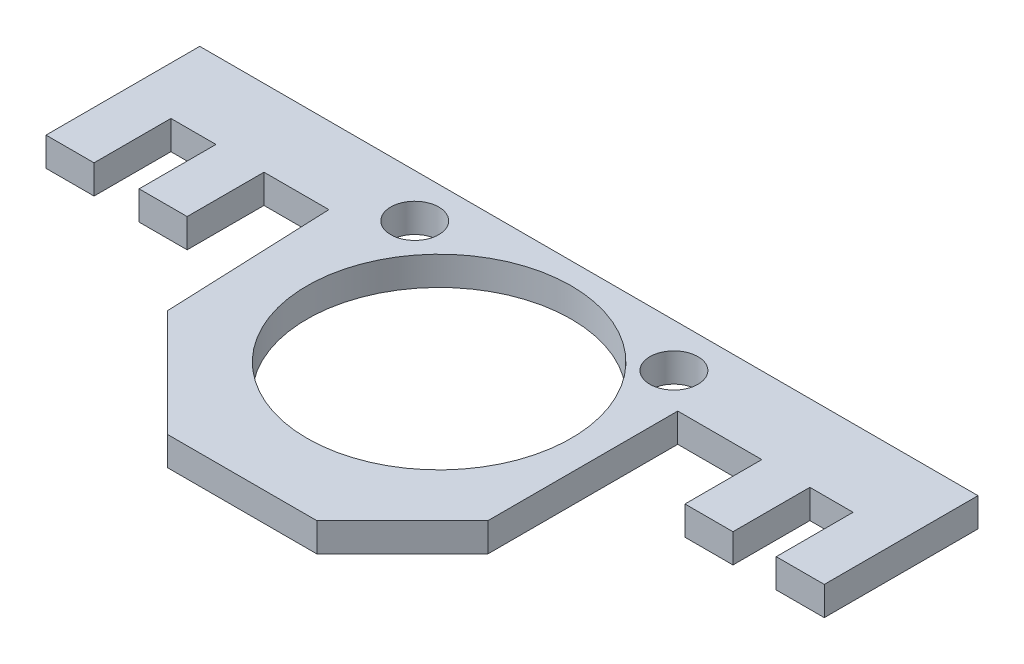
SolidWorks part; units mm, degrees
ref_plane "Front" through (0, 0, 0) normal (0, 0, 1) x (1, 0, 0)
ref_plane "Top" through (0, 0, 0) normal (0, 1, 0) x (1, 0, 0)
ref_plane "Right" through (0, 0, 0) normal (1, 0, 0) x (0, 0, -1)
sketch "Sketch1" plane through (0, 0, 0) normal (0, 1, 0) x (1, 0, 0)
  line L0 (-54.5899, 21.7003) -> (-22.1899, 21.7003)
  line L1 (-54.5899, 21.7003) -> (-54.5899, 15.3003)
  line L2 (-22.1899, 21.7003) -> (-22.1899, 15.3003)
  line L3 (-22.1899, 15.3003) -> (-24.1899, 15.3003)
  line L4 (-54.5899, 15.3003) -> (-52.5899, 15.3003)
  line L5 (-52.5899, 15.3003) -> (-52.5899, 18.5003)
  line L6 (-52.5899, 18.5003) -> (-50.714, 18.5003)
  line L7 (-50.714, 18.5003) -> (-50.714, 15.3003)
  line L8 (-50.714, 15.3003) -> (-48.714, 15.3003)
  line L9 (-48.714, 15.3003) -> (-48.714, 18.5003)
  line L10 (-48.714, 18.5003) -> (-46.014, 18.5003)
  line L12 (-24.1899, 15.3003) -> (-24.1899, 18.5003)
  line L13 (-24.1899, 18.5003) -> (-25.9899, 18.5003)
  line L14 (-25.9899, 18.5003) -> (-25.9899, 15.3003)
  line L15 (-25.9899, 15.3003) -> (-27.9899, 15.3003)
  line L16 (-27.9899, 15.3003) -> (-27.9899, 18.5003)
  line L17 (-27.9899, 18.5003) -> (-31.4899, 18.5003)
  line L22 (-31.4899, 18.5003) -> (-31.4899, 10.6003)
  line L23 (-31.4899, 10.6003) -> (-35.0537, 7.0365)
  line L24 (-35.0537, 7.0365) -> (-41.2737, 7.0365)
  line L25 (-41.2737, 7.0365) -> (-45.7285, 11.4913)
  line L26 (-45.7285, 11.4913) -> (-46.014, 18.5003)
extrude "Boss-Extrude1" add sketch "Sketch1" along normal blind 1.2
sketch "Sketch3" plane through (0, 1.2, 0) normal (0, 1, 0) x (1, 0, 0)
  line L0 (-22.1899, 15.3003) -> (-38.224, 15.3003) construction
  circle A2 centre (-43.8221, 19.8836) radius 1
  circle A3 centre (-33.0322, 19.8836) radius 1
  circle A4 centre (-38.224, 15.3003) radius 5.5
  point P3 (-32.8194, 19.5924)
  point P4 (0, 0)
  point P10 (0, 0)
  point P11 (-43.9173, 19.2214)
  point P12 (0, 0)
  point P13 (-43.7664, 20.3949)
  point P14 (-43.8421, 19.5924)
  point P15 (0, 0)
  point P16 (-31.561, 19.5924)
  point P17 (0, 0)
  point P18 (-33.007, 20.1191)
  point P19 (-33.0322, 19.8836)
  point P20 (-43.8221, 19.8836)
extrude "Cut-Extrude2" cut sketch "Sketch3" against normal up to next
